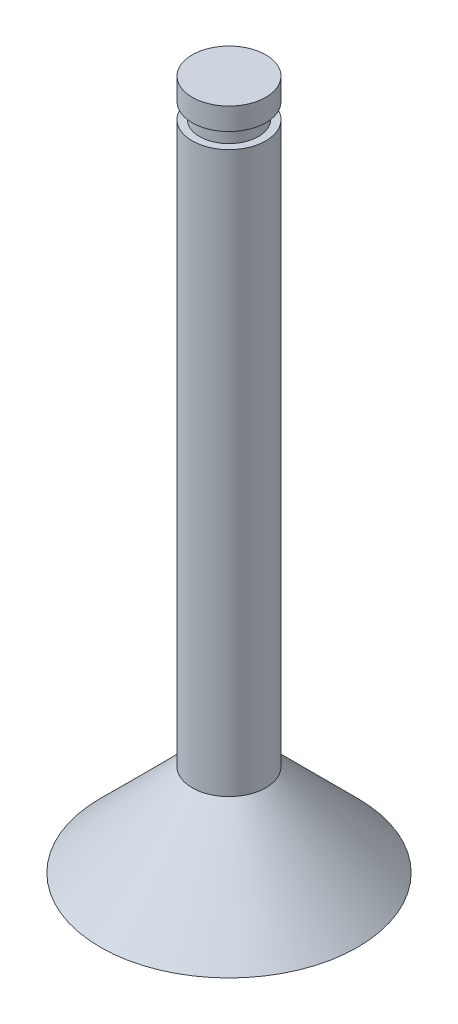
SolidWorks part; units mm, degrees
ref_plane "Přední rovina" through (0, 0, 0) normal (0, 0, 1) x (1, 0, 0)
ref_plane "Horní rovina" through (0, 0, 0) normal (0, 1, 0) x (1, 0, 0)
ref_plane "Pravá rovina" through (0, 0, 0) normal (1, 0, 0) x (0, 0, -1)
sketch "Skica1" plane through (0, 0, 0) normal (0, 0, 1) x (1, 0, 0)
  line L0 (0, 39.7321) -> (0, -28.3036) construction
  line L1 (0, 0) -> (7, 0)
  line L2 (7, 0) -> (2, 5)
  line L3 (2, 5) -> (2, 35.45)
  line L4 (2, 35.45) -> (1.6, 35.45)
  line L5 (1.6, 35.45) -> (1.6, 36.3)
  line L6 (1.6, 36.3) -> (2, 36.3)
  line L7 (2, 36.3) -> (2, 37.5)
  line L8 (2, 37.5) -> (0, 37.5)
  line L9 (0, 37.5) -> (0, 0)
  dimension "D1" = 5
  dimension "D2" = 14
  dimension "D3" = 4
  dimension "D4" = 45
  dimension "D5" = 37.5
  dimension "D6" = 0.85
  dimension "D7" = 1.2
  dimension "D8" = 3.2
revolve "Rotovat1" add sketch "Skica1" angle 360 about L0
